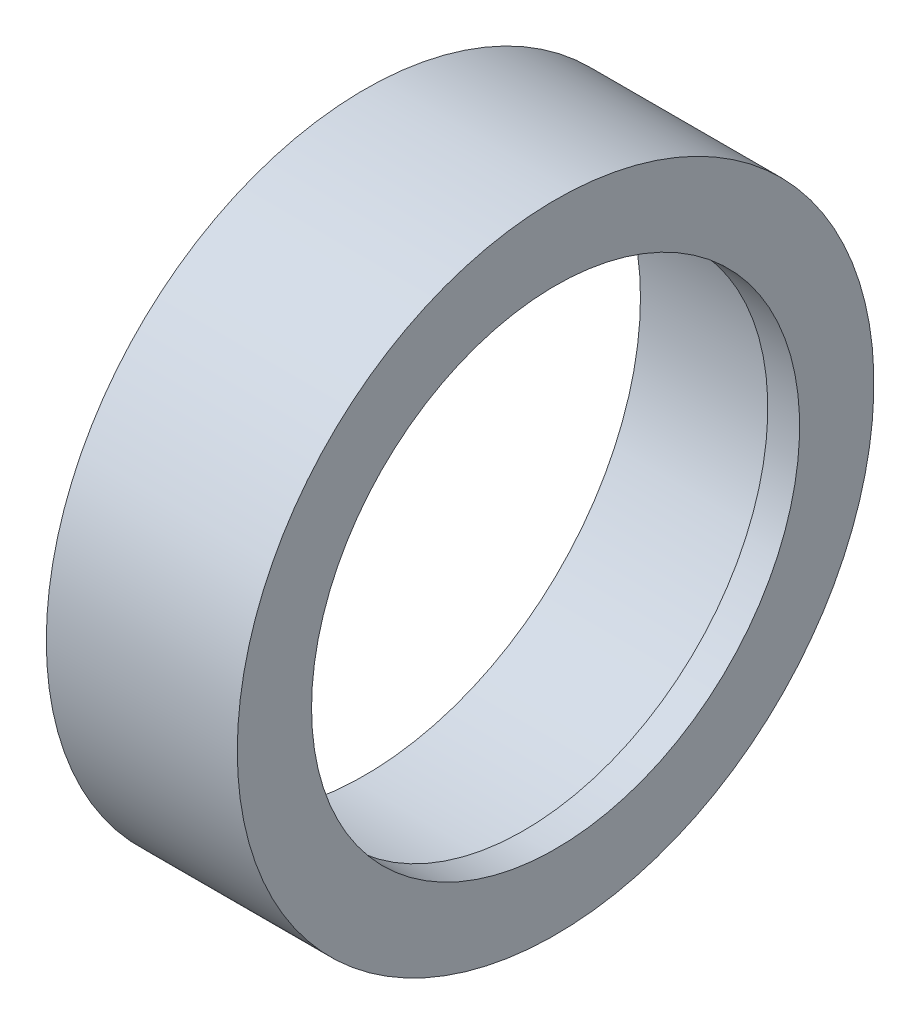
SolidWorks part; units mm, degrees
ref_plane "Спереди" through (0, 0, 0) normal (0, 0, 1) x (1, 0, 0)
ref_plane "Сверху" through (0, 0, 0) normal (0, 1, 0) x (1, 0, 0)
ref_plane "Справа" through (0, 0, 0) normal (1, 0, 0) x (0, 0, -1)
sketch "Подшипник" plane through (0, 0, 0) normal (0, 0, 1) x (1, 0, 0)
  line L0 (-1000, 0) -> (49000, 0) construction
  line L16 (0, 12.5) -> (-15, 12.5)
  line L17 (0, 12.5) -> (0, 26)
  line L18 (0, 26) -> (-15, 26)
  line L19 (-15, 12.5) -> (-15, 26)
  dimension "_d_" = 25
  dimension "_D" = 52
  dimension "_H" = 15
sketch "Бортик" plane through (0, 0, 0) normal (0, 0, 1) x (1, 0, 0)
  line L1 (0, 26) -> (3, 26)
  line L2 (0, 26) -> (0, 23)
  line L3 (0, 23) -> (3, 23)
  line L4 (3, 26) -> (3, 23)
  dimension "_H_бортика" = 3
  dimension "_L_боркика" = 3
sketch "Стопор 1" plane through (0, 0, 0) normal (0, 0, 1) x (1, 0, 0)
  line L0 (0, 26) -> (-15, 26) construction
  line L1 (-0.2, 26) -> (1.7, 26)
  line L2 (-0.2, 26) -> (-0.2, 27.5)
  line L3 (-0.2, 27.5) -> (1.7, 27.5)
  line L4 (1.7, 26) -> (1.7, 27.5)
  line L5 (0, 12.5) -> (0, 26) construction
  line L7 (-1000.2307, 0) -> (48999.7693, 0) construction
  dimension "_H_канавки" = 1.9
  dimension "_D_стопора" = 55
  dimension "_H_стопора" = 1.7
sketch "Стопор 2" plane through (0, 0, 0) normal (0, 0, 1) x (1, 0, 0)
  line L0 (0, 26) -> (-15, 26) construction
  line L1 (-14.8, 26) -> (-16.7, 26)
  line L2 (-14.8, 26) -> (-14.8, 27.5)
  line L3 (-14.8, 27.5) -> (-16.7, 27.5)
  line L4 (-16.7, 26) -> (-16.7, 27.5)
  line L5 (-0.2, 27.5) -> (1.7, 27.5) construction
  line L6 (-0.2, 26) -> (-0.2, 27.5) construction
  line L7 (1.7, 27.5) -> (0, 26) construction
  line L8 (-16.7, 27.5) -> (-15, 26) construction
sketch "Внешний диаметр обоймы" plane through (0, 0, 0) normal (0, 0, 1) x (1, 0, 0)
  line L0 (-21.2, 30) -> (6.2, 30)
  line L1 (-1000, 0) -> (49000, 0) construction
  line L3 (-16.7, 26) -> (-16.7, 27.5) construction
  line L4 (1.7, 26) -> (1.7, 27.5) construction
  dimension "_D_внешнего_диаметра _обоймы" = 60
  dimension "_L_мин_хвоста" = 4.5
  dimension "D1" = 4.5
sketch "Центровки" plane through (0, 0, 0) normal (0, 0, 1) x (1, 0, 0)
  line L0 (-21.2, 30) -> (6.2, 30) construction
  line L1 (-21.2, 30) -> (-18.2, 30)
  line L2 (-21.2, 30) -> (-21.2, 28)
  line L3 (-21.2, 28) -> (-18.2, 28)
  line L4 (-18.2, 30) -> (-18.2, 28)
  line L5 (6.2, 30) -> (3.2, 30)
  line L6 (6.2, 30) -> (6.2, 28)
  line L7 (6.2, 28) -> (3.2, 28)
  line L8 (3.2, 30) -> (3.2, 28)
  line L9 (3, 28) -> (0, 28)
  line L10 (3, 28) -> (3, 30)
  line L11 (3, 30) -> (0, 30)
  line L12 (0, 28) -> (0, 30)
  line L13 (3, 26) -> (3, 23) construction
  line L14 (-1000, 0) -> (49000, 0) construction
  dimension "_D_центровочный" = 56
  dimension "_L_центровочный" = 3
sketch "Удлиннение хвоста" plane through (0, 0, 0) normal (0, 0, 1) x (1, 0, 0)
  line L0 (-17, 30) -> (-17, 26)
  line L1 (-21.2, 30) -> (6.2, 30) construction
  line L2 (-15, 12.5) -> (-15, 26) construction
  line L3 (0, 26) -> (-15, 26) construction
  dimension "D1" = 2
sketch "Эскиз2" plane through (0, 0, 0) normal (0, 0, 1) x (1, 0, 0)
  line L0 (-15, 26) -> (-15, 30)
  line L1 (-21.2, 30) -> (6.2, 30) construction
  line L2 (-15, 30) -> (3, 30)
  line L3 (3, 30) -> (3, 23)
  line L4 (3, 23) -> (0, 23)
  line L5 (0, 23) -> (0, 26)
  line L6 (0, 26) -> (-15, 26)
  dimension "D1" = 18
revolve "Повернуть1" add sketch "Эскиз2" angle 360 about L0
equation "\"D1@Внешний диаметр обоймы\"=\"_L_мин_хвоста@Внешний диаметр обоймы\""
